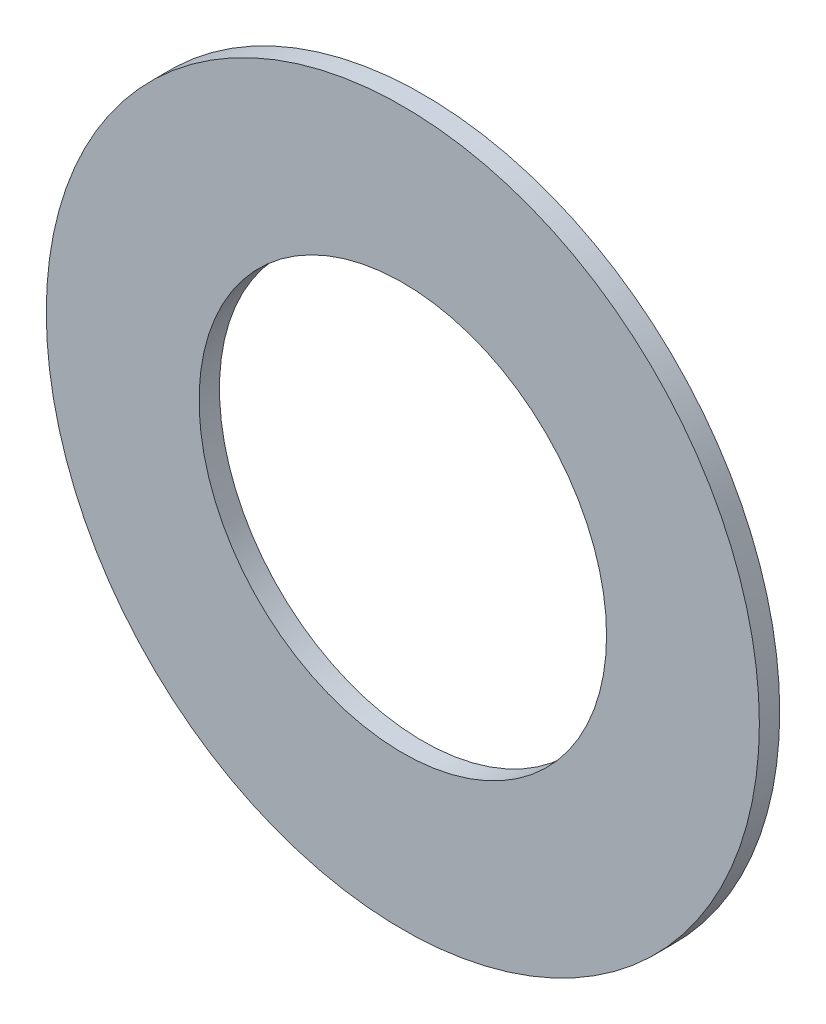
SolidWorks part; units mm, degrees
ref_plane "Front Plane" through (0, 0, 0) normal (0, 0, 1) x (1, 0, 0)
ref_plane "Top Plane" through (0, 0, 0) normal (0, 1, 0) x (1, 0, 0)
ref_plane "Right Plane" through (0, 0, 0) normal (1, 0, 0) x (0, 0, -1)
sketch "Sketch1" plane through (0, 0, 0) normal (0, 0, 1) x (1, 0, 0)
  circle A0 centre (0, 0) radius 10
  circle A1 centre (0, 0) radius 17.5
  dimension "D1" = 20
  dimension "D2" = 35
extrude "Boss-Extrude1" add sketch "Sketch1" along normal blind 1
